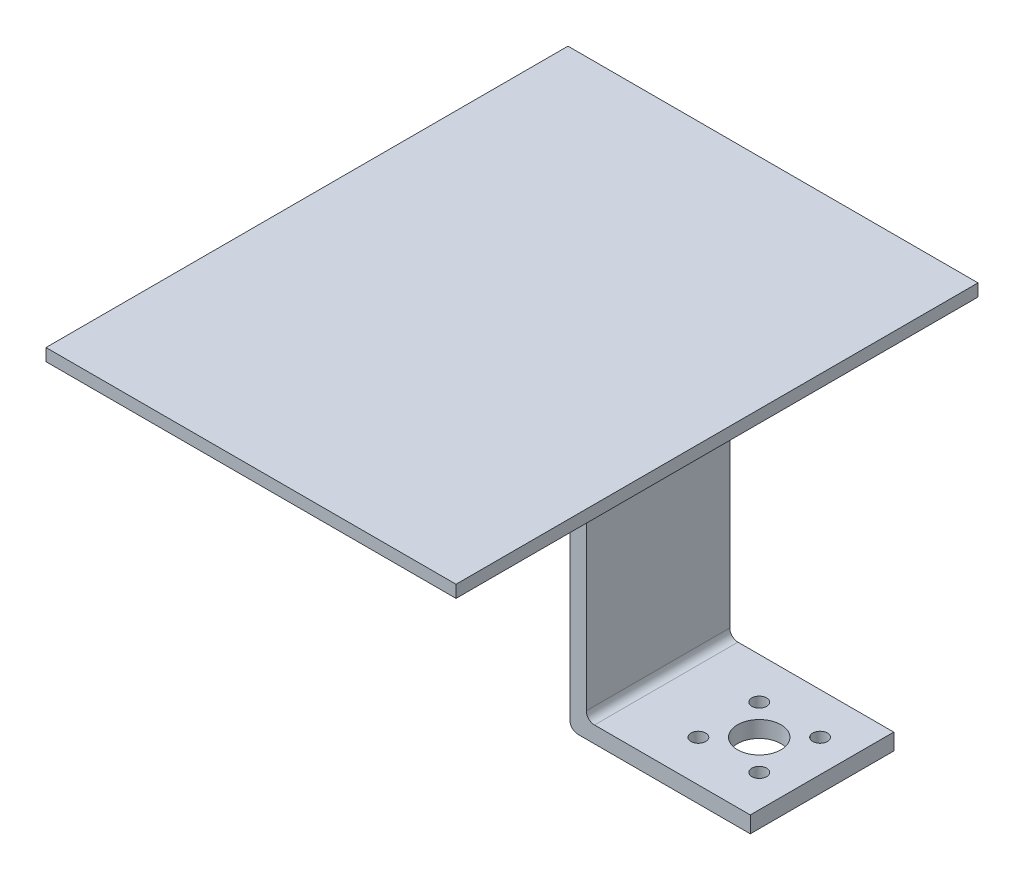
SolidWorks part; units mm, degrees
ref_plane "Alzado" through (0, 0, 0) normal (0, 0, 1) x (1, 0, 0)
ref_plane "Planta" through (0, 0, 0) normal (0, 1, 0) x (1, 0, 0)
ref_plane "Vista lateral" through (0, 0, 0) normal (1, 0, 0) x (0, 0, -1)
sketch "Croquis1" plane through (0, 0, 0) normal (0, 1, 0) x (1, 0, 0)
  line L1 (-50, 63.6524) -> (50, 63.6524)
  line L2 (-50, 63.6524) -> (-50, -63.6524)
  line L3 (-50, -63.6524) -> (50, -63.6524)
  line L4 (50, 63.6524) -> (50, -63.6524)
  line L5 (-50, 63.6524) -> (50, -63.6524) construction
  line L6 (-50, -63.6524) -> (50, 63.6524) construction
  point P0 (0, 0)
  dimension "D1" = 100
extrude "Saliente-Extruir1" add sketch "Croquis1" along normal blind 3
sketch "Croquis2" plane through (0, 0, 0) normal (0, -1, 0) x (1, 0, 0)
  line L0 (50, 0) -> (-50, 0) construction
  line L1 (35.6108, 17.4962) -> (31.6108, 17.4962)
  line L2 (35.6108, 17.4962) -> (35.6108, -17.4962)
  line L3 (35.6108, -17.4962) -> (31.6108, -17.4962)
  line L4 (31.6108, 17.4962) -> (31.6108, -17.4962)
  line L5 (50, 63.6524) -> (50, -63.6524) construction
  line L6 (-50, -63.6524) -> (-50, 63.6524) construction
  point P10 (35.6108, 0)
  dimension "D1" = 4
extrude "Saliente-Extruir2" add sketch "Croquis2" along normal blind 60
sketch "Croquis4" plane through (35.6108, 0, 0) normal (1, 0, 0) x (0, 0, -1)
  line L0 (-17.4962, -60) -> (-17.4962, 0) construction
  line L1 (-17.4962, -60) -> (17.4962, -60)
  line L2 (-17.4962, -60) -> (-17.4962, -56)
  line L3 (-17.4962, -56) -> (17.4962, -56)
  line L4 (17.4962, -60) -> (17.4962, -56)
  line L5 (17.4962, -60) -> (17.4962, 0) construction
  line L6 (17.4962, -60) -> (-17.4962, -60) construction
  dimension "D1" = 4
extrude "Saliente-Extruir3" add sketch "Croquis4" along normal blind 40
chamfer "Chaflán1" distance 10 angle 45 1 edges at (31.6108, 0, 0)
fillet "Redondeo1" radius 2 2 edges at (31.6108, -60, 0) (35.6108, -56, 0)
sketch "Croquis5" plane through (0, -60, 0) normal (0, -1, 0) x (1, 0, 0)
  line L0 (60.298, 0) -> (60.298, -10.5) construction
  line L1 (60.298, 0) -> (67.7227, -7.4246) construction
  line L2 (75.6108, 0) -> (48.57, 0) construction
  line L3 (75.6108, 17.4962) -> (75.6108, -17.4962) construction
  circle A0 centre (60.298, 0) radius 5.3
  circle A1 centre (60.298, 0) radius 10.5 construction
  circle A2 centre (67.7227, -7.4246) radius 1.8
  circle A3 centre (52.8734, -7.4246) radius 1.8
  circle A4 centre (52.8734, 7.4246) radius 1.8
  circle A5 centre (67.7227, 7.4246) radius 1.8
  point P20 (60.298, 0)
  dimension "D2" = 10.6
  dimension "D3" = 21
  dimension "D4" = 3.6
  dimension "D1" = 45
  dimension "D5" = 4
extrude "Cortar-Extruir2" cut sketch "Croquis5" against normal blind 40
